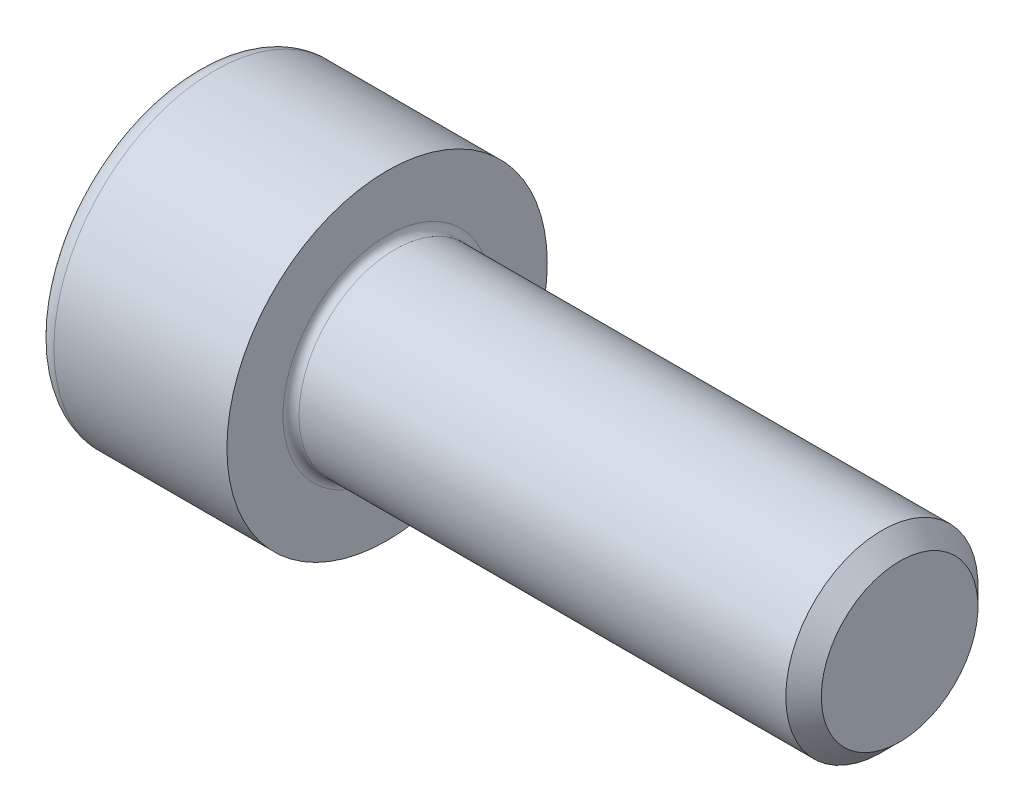
SolidWorks part; units mm, degrees
revolve "Base-Revolve" add sketch "BodySke"
sketch "BodySke" plane through (0, 0, 0) normal (0, 0, 1) x (1, 0, 0)
  line L0 (0, 0) -> (0, 5)
  line L1 (0, 5) -> (6, 5)
  line L2 (6, 5) -> (6, 3)
  line L3 (6, 3) -> (21.4455, 3)
  line L4 (22, 2.4455) -> (22, 0)
  line L5 (22, 0) -> (0, 0)
  line L6 (-31.75, 0) -> (127, 0) construction
  line L8 (22, 2.4455) -> (21.4455, 3)
  line L10 (22, -2.4455) -> (21.4455, -3) construction
  line L11 (7, 9.525) -> (7, 3.175) construction
  line L12 (6, 9.525) -> (6, 3.175) construction
  line L13 (-38, 9.525) -> (-38, 3.175) construction
  dimension "Body_ch_ang" = 45
  dimension "Thread_length" = 60
cosmetic thread "ThreadCosmetic" [suppressed]
fillet "Fillet1" radius 0.25 1 edges at (6, 0, 3)
fillet "Fillet2" radius 0.6 1 edges at (0, 0, 5)
ref_plane "Plane1" through (0, 0, 0) normal (0, 0, 1) x (1, 0, 0)
ref_plane "Plane2" through (0, 0, 0) normal (0, 1, 0) x (1, 0, 0)
ref_plane "Plane3" through (0, 0, 0) normal (1, 0, 0) x (0, 0, -1)
other "Configuration Table"
sketch "Sketch2" plane through (0, 0, 0) normal (0, 0, 1) x (1, 0, 0)
  line L0 (0, 2.51) -> (3, 2.51)
  line L1 (3, 2.51) -> (4.4491, 0)
  line L2 (-31.75, 0) -> (127, 0) construction
  line L3 (4.4491, 0) -> (0, 0)
  line L4 (0, 0) -> (0, 2.51)
  line L6 (0, 0) -> (47.625, 0) construction
  dimension "D2" = 60
revolve "Hex-PreBroach" cut sketch "Sketch2" angle 360 about L6
sketch "Sketch3" plane through (0, 0, 0) normal (-1, 0, 0) x (0, 0.5, 0.866)
  line L0 (1.4491, 2.51) -> (-1.4491, 2.51)
  line L1 (-1.4491, 2.51) -> (-2.8983, 0)
  line L2 (1.4491, 2.51) -> (2.8983, 0)
  line L3 (1.4491, -2.51) -> (2.8983, 0)
  line L4 (1.4491, -2.51) -> (-1.4491, -2.51)
  line L5 (-1.4491, -2.51) -> (-2.8983, 0)
extrude "Hex" cut sketch "Sketch3" against normal blind 3
sketch "ThdSchSke" plane through (0, 0, 0) normal (0, 0, 1) x (1, 0, 0)
  line L0 (9, -2.4455) -> (8.6117, -3)
  line L1 (9, -2.4455) -> (9.3883, -3)
  line L2 (9.3883, -3) -> (9.3883, -3.75)
  line L3 (-3.175, 0) -> (5.1513, 0) construction
  line L4 (0, 4.4) -> (0, -4.4) construction
  line L5 (9.3883, -3.75) -> (8.6117, -3.75)
  line L6 (8.6117, -3.75) -> (8.6117, -3)
revolve "ThreadSchematic" [suppressed] cut sketch "ThdSchSke" angle 360 about L3
pattern_linear "ThdSchPat" [suppressed]
equation "\"D2@Sketch3\" = \"Hex_size@Sketch3\" / 2"
equation "\"D1@Sketch3\" = \"Hex_size@Sketch3\" / 2"
equation "\"D1@Sketch2\" = \"Hex_size@Sketch3\" / 2"
equation "\"Thread_minor@ThreadCosmetic\"  =  \"Minor_dia@BodySke\""
equation "\"Depth@Sketch2\" =  \"Key_eng@Hex\""
equation "\"Thread_length@ThreadCosmetic\" = ((sgn( (\"Length@BodySke\" - \"Advance@BodySke\" * 3.0) - \"Thread_nom@BodySke\" )-1)*( (\"Length@BodySke\" - \"Advance@BodySke\" * 3.0) - \"Thread_nom@BodySke\" ))/-2+ \"Thread_nom@BodySke\""
equation "\"Thread_minor@ThdSchSke\" = \"Minor_dia@BodySke\""
equation "\"Diameter@ThdSchSke\" = \"Diameter@BodySke\""
equation "\"Overcut@ThdSchSke\" = \"Diameter@BodySke\" * 1.25"
equation "\"Start@ThdSchSke\" = \"Head_ht@BodySke\" + \"Length@BodySke\" - \"Thread_length@ThreadCosmetic\"  '---Non-countersunk---"
equation "\"Num_threads@ThdSchPat\" = int( \"Thread_length@ThreadCosmetic\" / \"Advance@BodySke\" + 0.999 )  + 1"
equation "\"Advance@ThdSchPat\" = \"Thread_length@ThreadCosmetic\" /  (\"Num_threads@ThdSchPat\" - 1) 'relax it"
equation "\"Num_threads@ThdSchPat\" = \"Num_threads@ThdSchPat\" - sgn( \"Num_threads@ThdSchPat\" - 1) '---chamfered tips only---"
